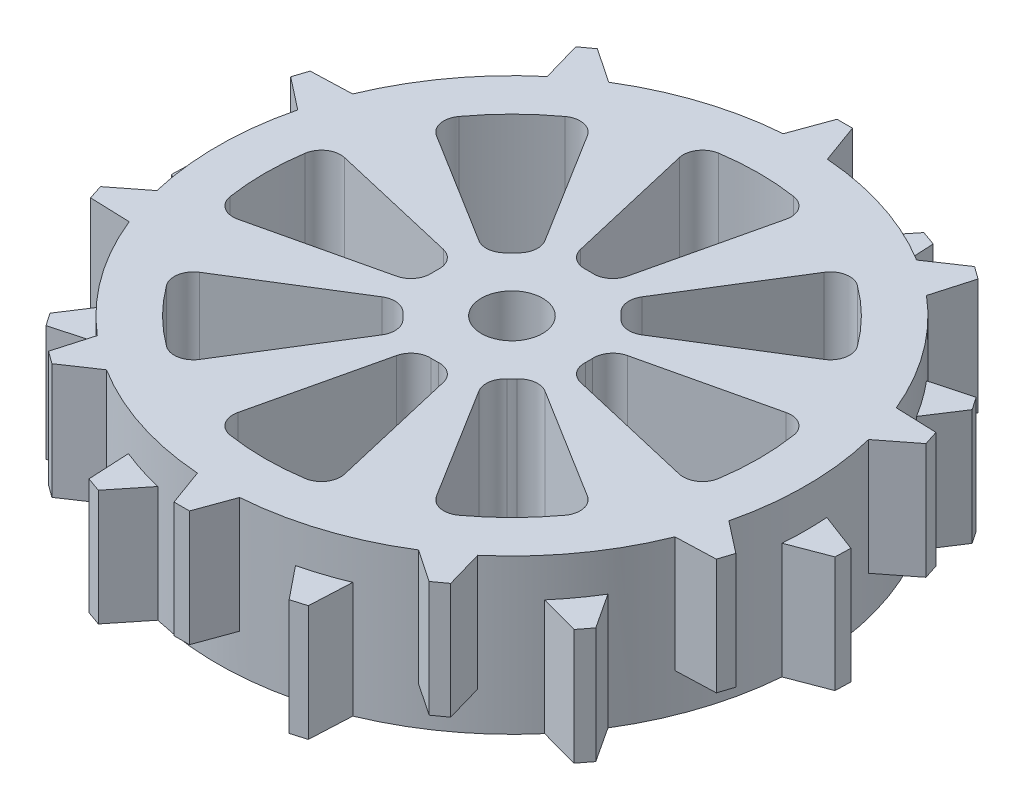
SolidWorks part; units mm, degrees
ref_plane "Front Plane" through (0, 0, 0) normal (0, 0, 1) x (1, 0, 0)
ref_plane "Top Plane" through (0, 0, 0) normal (0, 1, 0) x (1, 0, 0)
ref_plane "Right Plane" through (0, 0, 0) normal (1, 0, 0) x (0, 0, -1)
sketch "Sketch1" plane through (0, 0, 0) normal (0, 1, 0) x (1, 0, 0)
  circle A0 centre (0, 0) radius 76.2
  dimension "D1" = 152.4
extrude "Boss-Extrude1" add sketch "Sketch1" along normal blind 40
sketch "Sketch2" plane through (0, 40, 0) normal (0, 1, 0) x (1, 0, 0)
  line L0 (0, 76.2) -> (0, 86.2)
  line L1 (0, 86.2) -> (-2, 86.2)
  line L2 (-2, 86.2) -> (-5.7179, 75.9852)
  line L3 (0, 86.2) -> (2, 86.2)
  line L4 (2, 86.2) -> (5.7179, 75.9852)
  circle A0 centre (0, 0) radius 76.2 construction
  circle A1 centre (0, 0) radius 76.2
  circle M7 centre (0, 0) radius 76.2
  dimension "D1" = 20
  dimension "D2" = 20
  dimension "D3" = 2
  dimension "D4" = 2
  dimension "D5" = 10
extrude "Boss-Extrude2" add sketch "Sketch2" against normal blind 30 contours L4 L3 L0 M7 | L1 L2 L0 M7
pattern_circular "CirPattern1" count 10 over 360 about axis through (0, 0, -0.3387) along (0, 1, 0) of "Boss-Extrude2"
sketch "Sketch3" plane through (0, 0, 0) normal (0, -1, 0) x (1, 0, 0)
  line L0 (17.9805, 74.0482) -> (24.8116, 82.5155)
  line L1 (24.8116, 82.5155) -> (28.6489, 81.3861)
  line L2 (28.6489, 81.3861) -> (29.1781, 70.3923)
  line L3 (0, 0) -> (23.6293, 72.4437)
  line L4 (0, 0) -> (0, 85.5227)
  line L5 (2, 85.5227) -> (-2, 85.5227) construction
  line L6 (0, 0) -> (-50.468, 69.1246)
  line L7 (-48.85, 70.3002) -> (-52.0861, 67.9491) construction
  line L8 (26.7303, 81.9508) -> (23.6293, 72.4437)
  circle A0 centre (0, 0) radius 76.2
  point P5 (0, 0)
  circle M10 centre (0, 0) radius 76.2
  dimension "D1" = 36.133
  dimension "D6" = 152.4
  dimension "D2" = 18.065
  dimension "D3" = 4
  dimension "D4" = 10
extrude "Boss-Extrude3" add sketch "Sketch3" against normal blind 30 contours L8 L1 L0 M10 | L1 L8 L2 M10
pattern_circular "CirPattern2" count 10 over 360 about axis through (0.1074, 0, 0.3289) along (0, 1, 0) of "Boss-Extrude3"
sketch "Sketch4" plane through (0, 40, 0) normal (0, 1, 0) x (1, 0, 0)
  circle A0 centre (0, 0) radius 7.9375
  dimension "D1" = 15.875
extrude "Cut-Extrude1" cut sketch "Sketch4" against normal through all
sketch "Sketch5" plane through (0, 40, 0) normal (0, 1, 0) x (1, 0, 0)
  line L0 (-15, 62.2174) -> (-5, 19.3649)
  line L1 (5, 19.3649) -> (15, 62.2174)
  circle A0 centre (0, 0) radius 64
  circle A1 centre (0, 0) radius 20
  dimension "D1" = 128
  dimension "D6" = 40
  dimension "D2" = 15
  dimension "D3" = 15
  dimension "D4" = 5
  dimension "D5" = 5
extrude "Cut-Extrude2" cut sketch "Sketch5" against normal through all contours A1 L1 A0 L0
pattern_circular "CirPattern3" count 8 over 360 about axis through (0, 0, 0) along (0, 1, 0) of "Cut-Extrude2"
fillet "Fillet4" radius 5 24 edges at (33.3877, 20, 54.6009) (-15, 20, 62.2174) (-54.6009, 20, 33.3877) (-62.2174, 20, -15) (-33.3877, 20, -54.6009) (15, 20, -62.2174) (54.6009, 20, -33.3877) (62.2174, 20, 15) (-19.3649, 20, 5) (-19.3649, 20, -5) (-17.2286, 20, -10.1575) (-10.1575, 20, -17.2286) (5, 20, -19.3649) (-5, 20, -19.3649) (10.1575, 20, -17.2286) (17.2286, 20, -10.1575) (19.3649, 20, -5) (19.3649, 20, 5) (-10.1575, 20, 17.2286) (-17.2286, 20, 10.1575) (-5, 20, 19.3649) (5, 20, 19.3649) (17.2286, 20, 10.1575) (10.1575, 20, 17.2286)
fillet "Fillet5" radius 5 8 edges at (-33.3877, 20, 54.6009) (15, 20, 62.2174) (-62.2174, 20, 15) (-54.6009, 20, -33.3877) (-15, 20, -62.2174) (33.3877, 20, -54.6009) (62.2174, 20, -15) (54.6009, 20, 33.3877)
